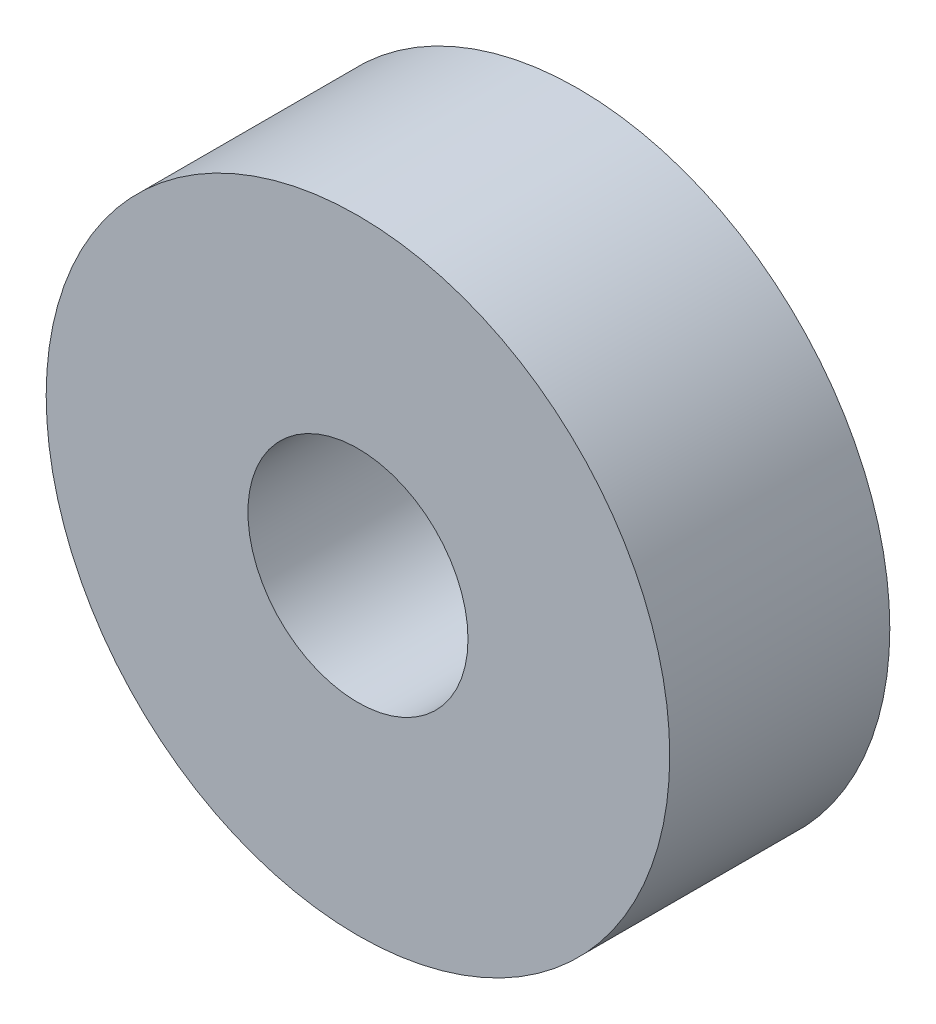
SolidWorks part; units mm, degrees
ref_plane "Front Plane" through (0, 0, 0) normal (0, 0, 1) x (1, 0, 0)
ref_plane "Top Plane" through (0, 0, 0) normal (0, 1, 0) x (1, 0, 0)
ref_plane "Right Plane" through (0, 0, 0) normal (1, 0, 0) x (0, 0, -1)
sketch "Sketch1" plane through (0, 0, 0) normal (0, 0, 1) x (1, 0, 0)
  circle A0 centre (0, 0) radius 8.5
  circle A1 centre (0, 0) radius 3
  dimension "D1" = 17
  dimension "D2" = 6
extrude "Boss-Extrude1" add sketch "Sketch1" along normal mid plane 6
